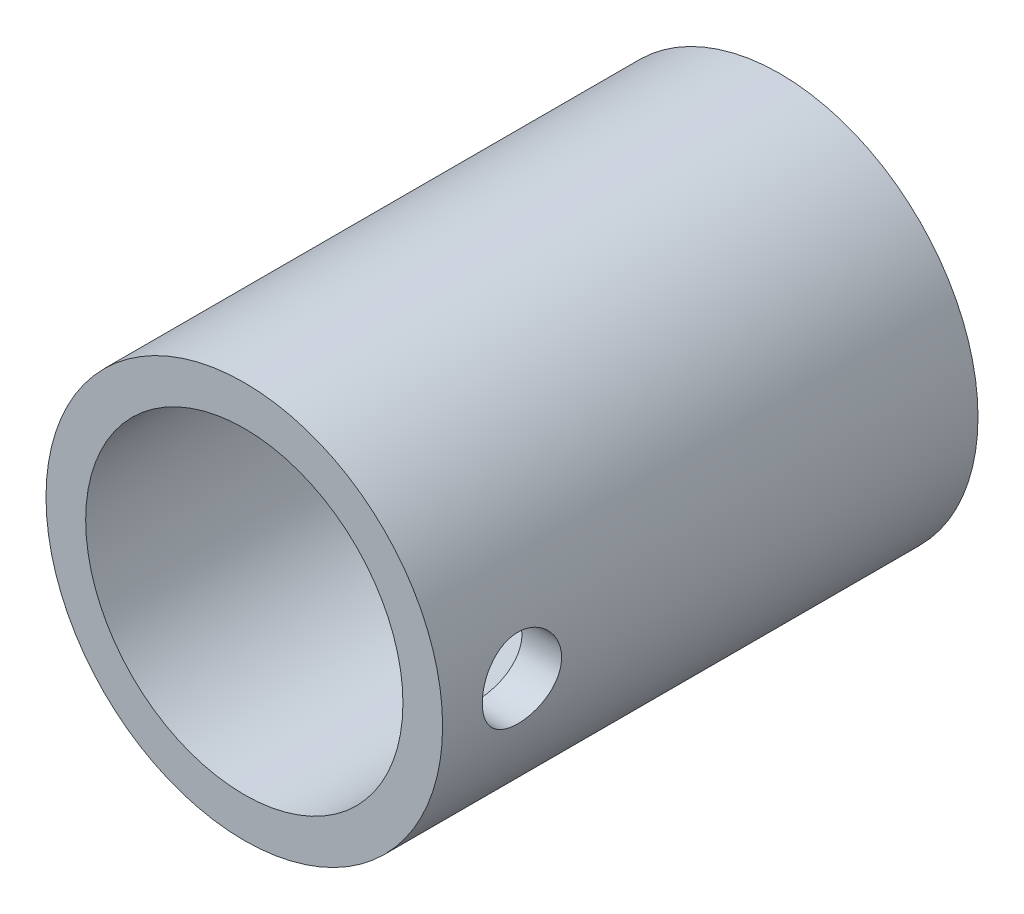
SolidWorks part; units mm, degrees
material "Stainless Steel (ferritic)"
ref_plane "Front Plane" through (0, 0, 0) normal (0, 0, 1) x (1, 0, 0)
ref_plane "Top Plane" through (0, 0, 0) normal (0, 1, 0) x (1, 0, 0)
ref_plane "Right Plane" through (0, 0, 0) normal (1, 0, 0) x (0, 0, -1)
sketch "Sketch2" plane through (0, 0, 0) normal (0, 0, 1) x (1, 0, 0)
  circle A0 centre (0, 0) radius 4
  circle A1 centre (0, 0) radius 5
  dimension "D1" = 8
  dimension "D2" = 10
extrude "Boss-Extrude1" add sketch "Sketch2" along normal blind 13.5
sketch "Sketch3" plane through (0, 0, 0) normal (1, 0, 0) x (0, 0, -1)
  circle A0 centre (-11.5, 0) radius 1
  dimension "D1" = 2
  dimension "D2" = 11.5
extrude "Cut-Extrude1" cut sketch "Sketch3" along normal blind 6.5
